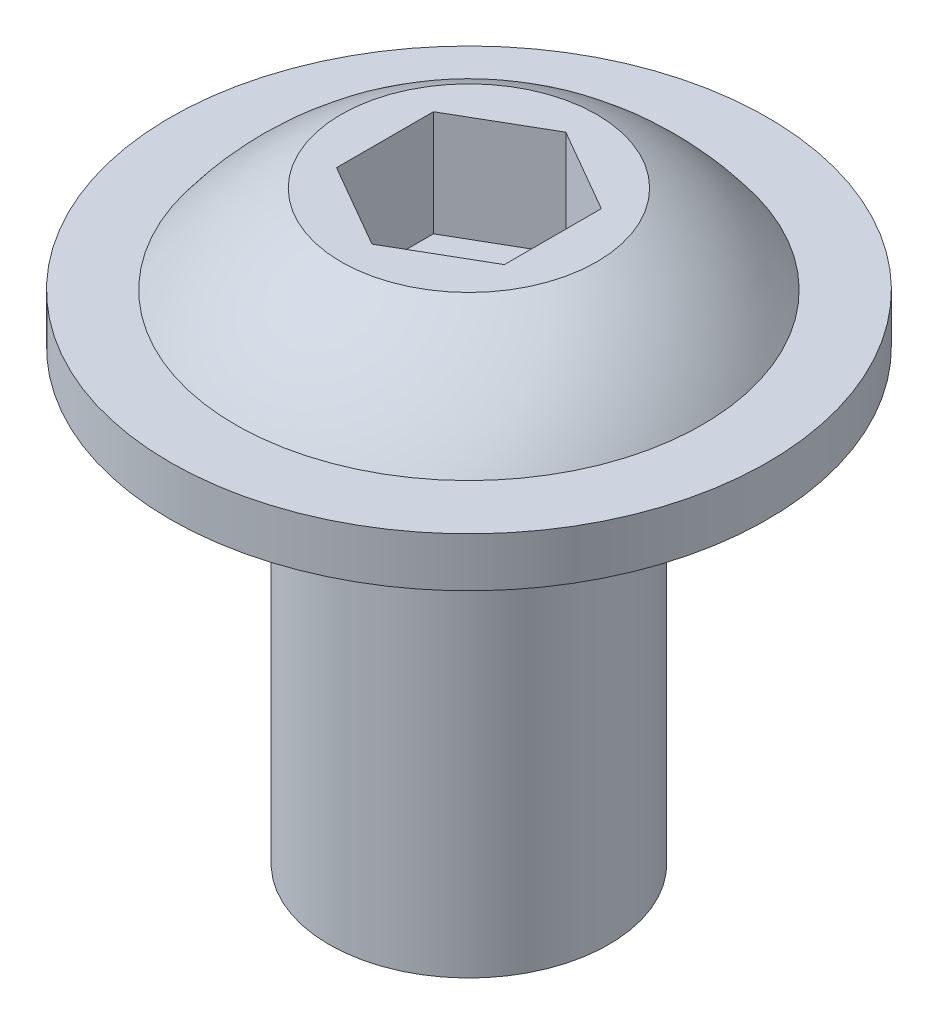
SolidWorks part; units mm, degrees
ref_plane "Front Plane" through (0, 0, 0) normal (0, 0, 1) x (1, 0, 0)
ref_plane "Top Plane" through (0, 0, 0) normal (0, 1, 0) x (1, 0, 0)
ref_plane "Right Plane" through (0, 0, 0) normal (1, 0, 0) x (0, 0, -1)
sketch "Sketch1" plane through (0, 0, 0) normal (0, 1, 0) x (1, 0, 0)
  circle A0 centre (0, 0) radius 3.9688
  dimension "D1" = 7.9375
extrude "Boss-Extrude1" add sketch "Sketch1" along normal blind 12.7
sketch "Sketch2" plane through (0, 12.7, 0) normal (0, 1, 0) x (1, 0, 0)
  circle A0 centre (0, 0) radius 8.475
  dimension "D1" = 16.95
extrude "Boss-Extrude2" add sketch "Sketch2" along normal blind 1.4
sketch "Sketch3" plane through (0, 0, 0) normal (0, 0, 1) x (1, 0, 0)
  line L0 (8.475, 14.1) -> (-8.475, 14.1) construction
  line L1 (8.475, 14.1) -> (6.625, 14.1) construction
  line L2 (-3.625, 16.6) -> (0, 16.6)
  line L3 (0, 16.6) -> (0, 14.1) construction
  line L4 (-6.625, 14.1) -> (0, 14.1)
  line L5 (0, 14.1) -> (-8.475, 14.1) construction
  line L6 (0, 16.6) -> (0, 14.1)
  arc A0 (-6.625, 14.1) -> (-3.625, 16.6) centre (0, 9.2) cw
  dimension "D4" = 8.2402
  dimension "D1" = 13.25
  dimension "D2" = 2.5
  dimension "D3" = 3.625
  dimension "D5" = 6.625
revolve "Revolve2" add sketch "Sketch3" angle 360 about L3
sketch "Sketch4" plane through (0, 16.6, 0) normal (0, 1, 0) x (1, 0, 0)
  line L1 (-2.3813, 1.3748) -> (-2.3813, -1.3748)
  line L2 (-2.3813, -1.3748) -> (0, -2.7496)
  line L3 (0, -2.7496) -> (2.3813, -1.3748)
  line L4 (2.3813, -1.3748) -> (2.3813, 1.3748)
  line L5 (2.3813, 1.3748) -> (0, 2.7496)
  line L6 (0, 2.7496) -> (-2.3813, 1.3748)
  circle A0 centre (0, 0) radius 2.3813 construction
  dimension "D1" = 4.7625
extrude "Cut-Extrude1" cut sketch "Sketch4" against normal blind 3
